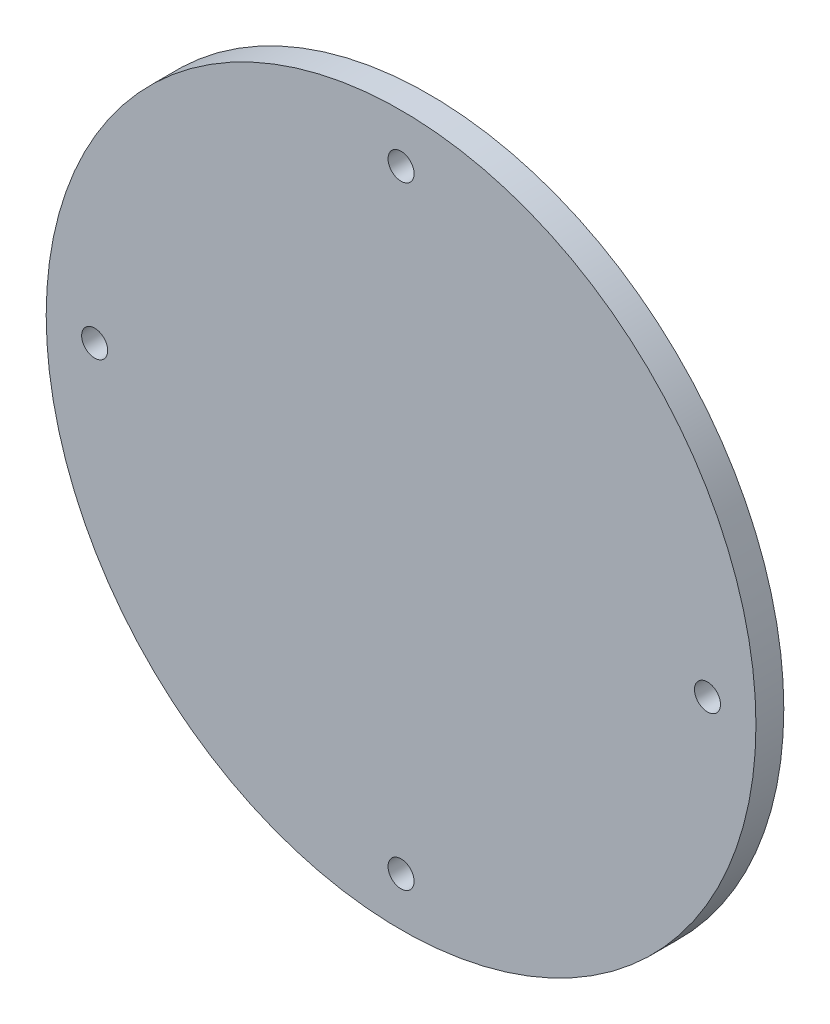
SolidWorks part; units mm, degrees
material "Acrylic (Medium-high impact)"
ref_plane "Front Plane" through (0, 0, 0) normal (0, 0, 1) x (1, 0, 0)
ref_plane "Top Plane" through (0, 0, 0) normal (0, 1, 0) x (1, 0, 0)
ref_plane "Right Plane" through (0, 0, 0) normal (1, 0, 0) x (0, 0, -1)
sketch "Sketch1" plane through (0, 0, 0) normal (0, 0, 1) x (1, 0, 0)
  circle A0 centre (0, 0) radius 63.7004
  circle A1 centre (0, 55) radius 2.3357
  circle A2 centre (55, 0) radius 2.3357
  circle A3 centre (0, -55) radius 2.3357
  circle A4 centre (-55, 0) radius 2.3357
  point P13 (0, 0)
  dimension "D1" = 55
  dimension "D2" = 4
extrude "Boss-Extrude1" add sketch "Sketch1" along normal blind 5
